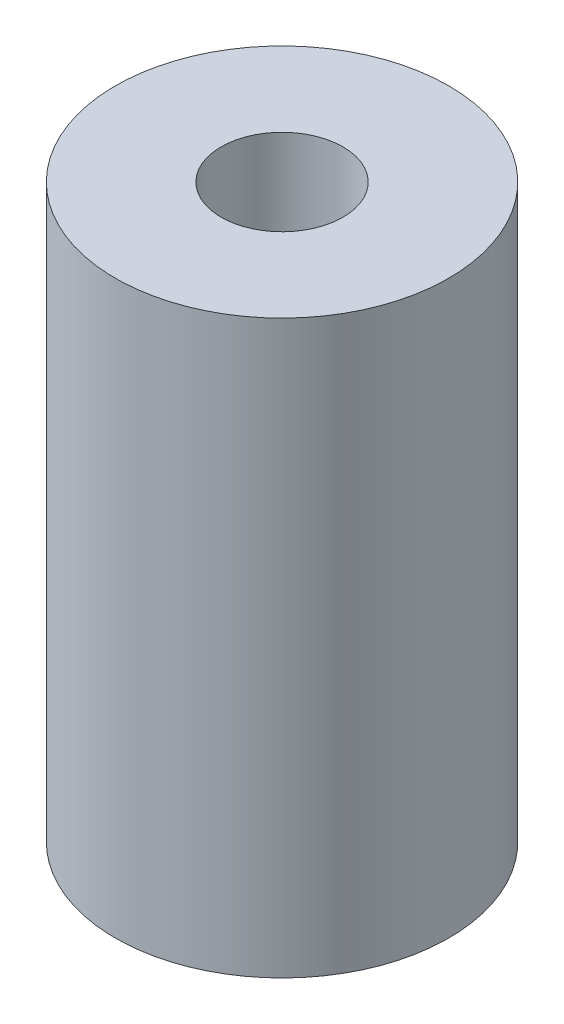
SolidWorks part; units mm, degrees
ref_plane "Front Plane" through (0, 0, 0) normal (0, 0, 1) x (1, 0, 0)
ref_plane "Top Plane" through (0, 0, 0) normal (0, 1, 0) x (1, 0, 0)
ref_plane "Right Plane" through (0, 0, 0) normal (1, 0, 0) x (0, 0, -1)
sketch "Sketch2" plane through (0, 0, 0) normal (0, 0, 1) x (1, 0, 0)
  line L0 (0, 0) -> (4.064, 0) construction
  line L2 (4.064, 0) -> (11.1125, 0)
  line L3 (4.064, 0) -> (4.064, 38.1)
  line L4 (4.064, 38.1) -> (11.1125, 38.1)
  line L8 (11.1125, 0) -> (11.1125, 38.1)
  line L9 (0, 0) -> (0, 30.073) construction
  point P9 (0, 0)
  dimension "D1" = 4.064
  dimension "D2" = 38.1
revolve "Revolve1" add sketch "Sketch2" angle 360 about L9
